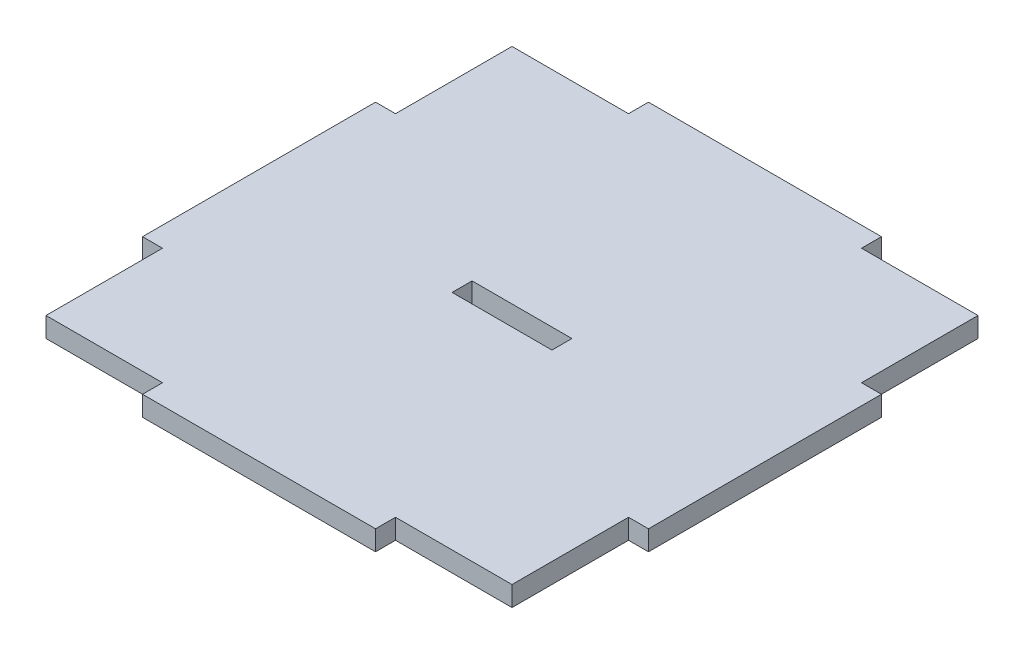
SolidWorks part; units mm, degrees
ref_plane "Front Plane" through (0, 0, 0) normal (0, 0, 1) x (1, 0, 0)
ref_plane "Top Plane" through (0, 0, 0) normal (0, 1, 0) x (1, 0, 0)
ref_plane "Right Plane" through (0, 0, 0) normal (1, 0, 0) x (0, 0, -1)
sketch "Sketch1" plane through (0, 0, 0) normal (0, 1, 0) x (1, 0, 0)
  line L0 (0, 35) -> (0, -35) construction
  line L1 (-35, -35) -> (-17.5, -35)
  line L2 (-35, -35) -> (-35, -17.5)
  line L3 (-35, 35) -> (-17.5, 35)
  line L4 (35, -35) -> (35, -17.5)
  line L5 (-35, -35) -> (35, 35) construction
  line L6 (-35, 35) -> (35, -35) construction
  line L11 (-38, -38) -> (38, 38) construction
  line L12 (-38, 38) -> (38, -38) construction
  line L13 (-35, 0) -> (35, 0) construction
  line L14 (-17.5, 38) -> (-17.5, 35)
  line L15 (-38, 17.5) -> (-35, 17.5)
  line L16 (17.5, 38) -> (17.5, 35)
  line L17 (-38, -17.5) -> (-35, -17.5)
  line L18 (38, 17.5) -> (35, 17.5)
  line L19 (38, -17.5) -> (35, -17.5)
  line L20 (17.5, -38) -> (17.5, -35)
  line L21 (-17.5, -38) -> (-17.5, -35)
  line L22 (-38, -17.5) -> (-38, 17.5)
  line L23 (38, 17.5) -> (38, -17.5)
  line L24 (-17.5, -38) -> (17.5, -38)
  line L25 (-17.5, 38) -> (17.5, 38)
  line L26 (17.5, 35) -> (35, 35)
  line L27 (35, 17.5) -> (35, 35)
  line L28 (17.5, -35) -> (35, -35)
  line L29 (-35, 17.5) -> (-35, 35)
  point P0 (0, 0)
  point P6 (0, 0)
  dimension "D1" = 76
  dimension "D2" = 70
  dimension "D3" = 76
  dimension "D4" = 70
  dimension "D5" = 17.5
  dimension "D6" = 17.5
  dimension "D7" = 3
  dimension "D8" = 3
extrude "Boss-Extrude1" add sketch "Sketch1" along normal blind 3
sketch "Sketch2" plane through (0, 3, 0) normal (0, 1, 0) x (1, 0, 0)
  line L1 (-7.5, -1.5) -> (7.5, -1.5)
  line L2 (-7.5, -1.5) -> (-7.5, 1.5)
  line L3 (-7.5, 1.5) -> (7.5, 1.5)
  line L4 (7.5, -1.5) -> (7.5, 1.5)
  line L5 (-7.5, -1.5) -> (7.5, 1.5) construction
  line L6 (-7.5, 1.5) -> (7.5, -1.5) construction
  point P0 (0, 0)
  dimension "D1" = 15
  dimension "D2" = 3
extrude "Cut-Extrude1" cut sketch "Sketch2" against normal blind 3
